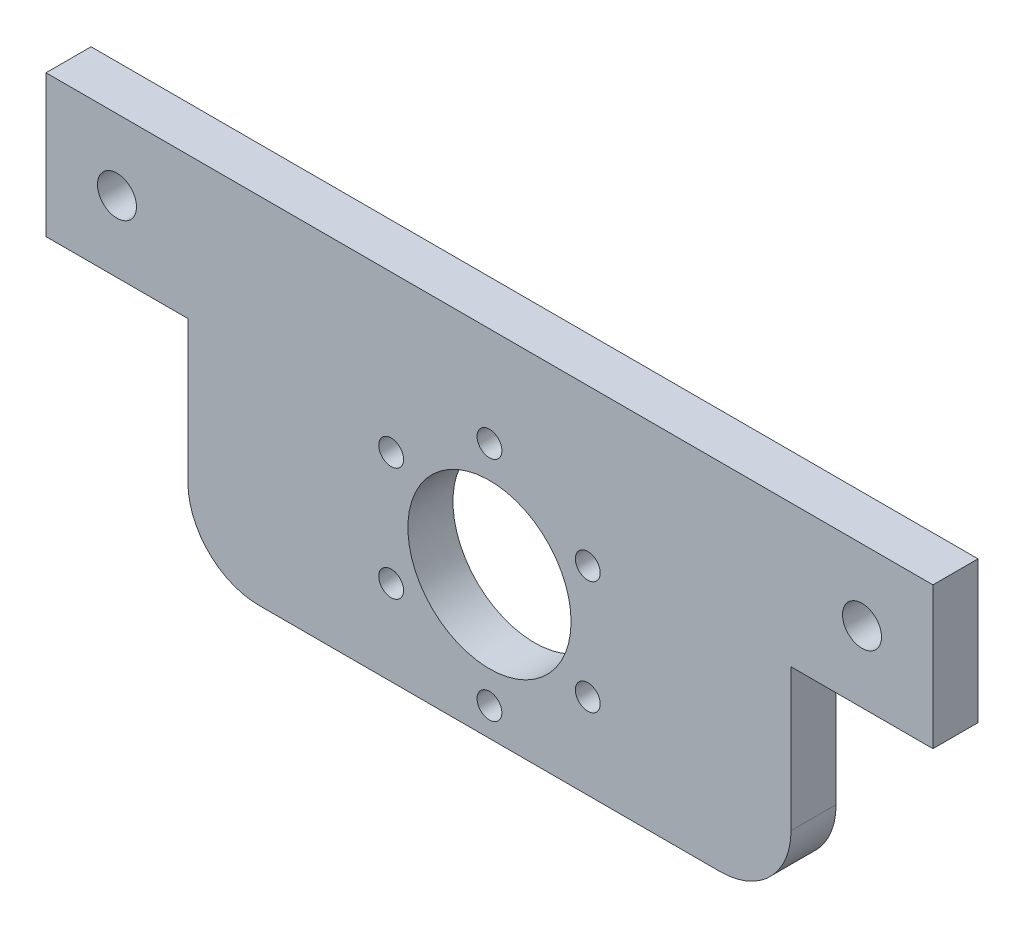
SolidWorks part; units mm, degrees
ref_plane "Front Plane" through (0, 0, 0) normal (0, 0, 1) x (1, 0, 0)
ref_plane "Top Plane" through (0, 0, 0) normal (0, 1, 0) x (1, 0, 0)
ref_plane "Right Plane" through (0, 0, 0) normal (1, 0, 0) x (0, 0, -1)
sketch "Sketch1" plane through (0, 0, 0) normal (0, 0, 1) x (1, 0, 0)
  line L1 (0, 0) -> (125, 0)
  line L2 (0, 0) -> (0, 50)
  line L3 (0, 50) -> (125, 50)
  line L4 (125, 0) -> (125, 50)
  dimension "D1" = 50
  dimension "D2" = 125
extrude "Boss-Extrude1" add sketch "Sketch1" along normal blind 6.35
sketch "Sketch2" plane through (0, 0, 6.35) normal (0, 0, 1) x (1, 0, 0)
  line L3 (0, 0) -> (125, 0) construction
  line L4 (62.5, 0) -> (62.5, 59.4224) construction
  line L5 (0, 0) -> (125, 0) construction
  circle A0 centre (62.5, 20) radius 11.5
  point P10 (0, 0)
  dimension "D1" = 23
  dimension "D2" = 20
extrude "Cut-Extrude1" cut sketch "Sketch2" against normal through all
sketch "Sketch5" plane through (0, 0, 0) normal (0, 0, -1) x (-1, 0, 0)
  circle A0 centre (-48.6436, 28) radius 1.75
  circle A1 centre (-48.6436, 12) radius 1.75
  circle A2 centre (-62.5, 4) radius 1.75
  circle A3 centre (-76.3564, 12) radius 1.75
  circle A4 centre (-76.3564, 28) radius 1.75
  circle A5 centre (-62.5, 36) radius 1.75
  circle A6 centre (-62.5, 20) radius 11.5 construction
  point P2 (0, 0)
  point P22 (-62.5, 20)
  dimension "D1" = 16
  dimension "D3" = 3.5
  dimension "D2" = 6
extrude "Cut-Extrude5" cut sketch "Sketch5" against normal through all
sketch "Sketch6" plane through (0, 0, 0) normal (0, 0, -1) x (-1, 0, 0)
  line L0 (0, 50) -> (0, 0) construction
  line L1 (-125, 25) -> (0, 25) construction
  line L2 (-125, 0) -> (-125, 50) construction
  line L5 (-125, 0) -> (-105, 0)
  line L6 (-125, 0) -> (-125, 30)
  line L7 (-125, 30) -> (-105, 30)
  line L8 (-105, 0) -> (-105, 30)
  line L9 (0, 0) -> (-20, 0)
  line L10 (0, 0) -> (0, 30)
  line L11 (0, 30) -> (-20, 30)
  line L12 (-20, 0) -> (-20, 30)
  circle A0 centre (-115, 40) radius 2.75
  circle A1 centre (-10, 40) radius 2.75
  point P12 (-115, 30)
  dimension "D3" = 5.5
  dimension "D4" = 5.5
  dimension "D1" = 10
  dimension "D2" = 10
  dimension "D5" = 10
  dimension "D6" = 20
  dimension "D7" = 30
  dimension "D8" = 20
  dimension "D9" = 30
extrude "Cut-Extrude6" cut sketch "Sketch6" against normal through all
fillet "Fillet1" radius 10 2 edges at (20, 0, 3.175) (105, 0, 3.175)
